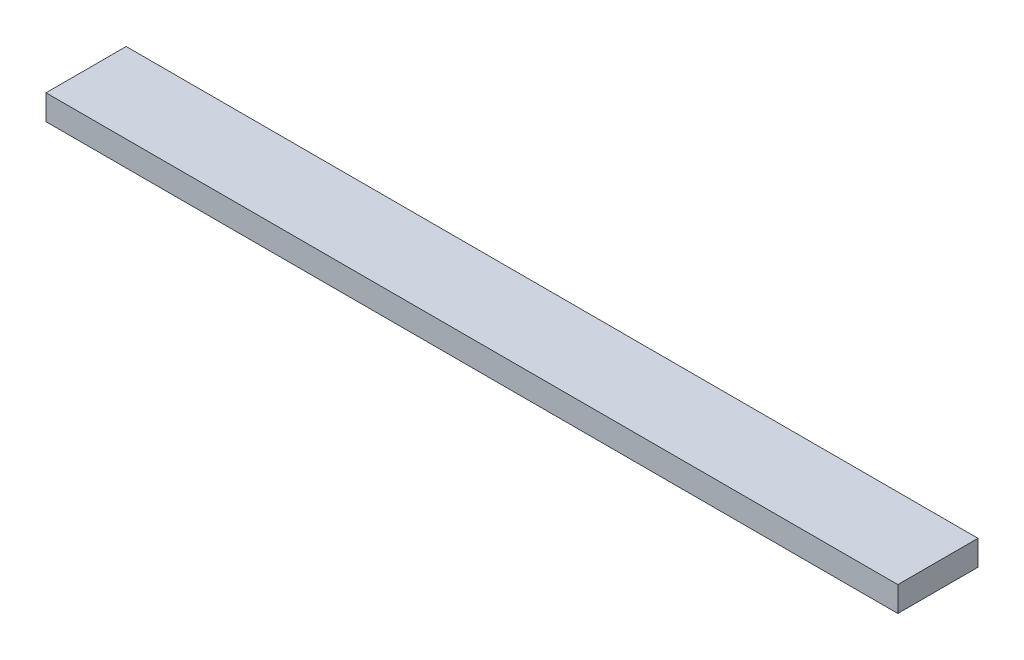
SolidWorks part; units mm, degrees
ref_plane "Спереди" through (0, 0, 0) normal (0, 0, 1) x (1, 0, 0)
ref_plane "Сверху" through (0, 0, 0) normal (0, 1, 0) x (1, 0, 0)
ref_plane "Справа" through (0, 0, 0) normal (1, 0, 0) x (0, 0, -1)
sketch "Эскиз1" plane through (0, 0, 0) normal (1, 0, 0) x (0, 0, -1)
  line L1 (-40, 12.5) -> (40, 12.5)
  line L2 (-40, 12.5) -> (-40, -12.5)
  line L3 (-40, -12.5) -> (40, -12.5)
  line L4 (40, 12.5) -> (40, -12.5)
  line L5 (-40, 12.5) -> (40, -12.5) construction
  line L6 (-40, -12.5) -> (40, 12.5) construction
  point P0 (0, 0)
extrude "Бобышка-Вытянуть1" add sketch "Эскиз1" along normal blind 850
